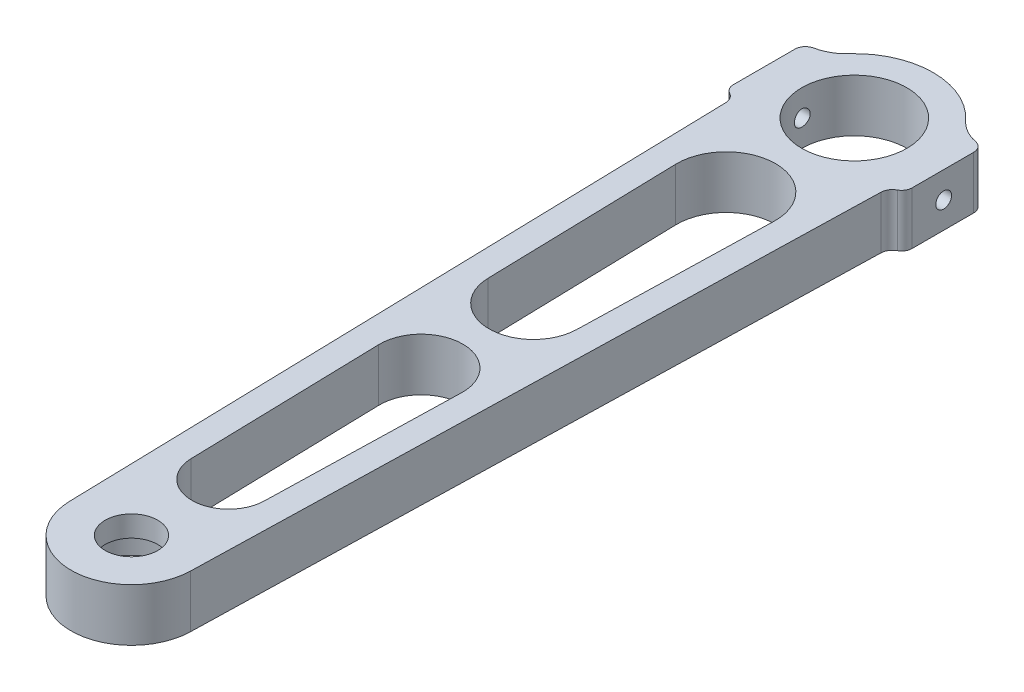
SolidWorks part; units mm, degrees
material "6061 Alloy"
ref_plane "Front Plane" through (0, 0, 0) normal (0, 0, 1) x (1, 0, 0)
ref_plane "Top Plane" through (0, 0, 0) normal (0, 1, 0) x (1, 0, 0)
ref_plane "Right Plane" through (0, 0, 0) normal (1, 0, 0) x (0, 0, -1)
sketch "Sketch1" plane through (0, 0, 0) normal (0, 1, 0) x (1, 0, 0)
  line L0 (-14.7582, -9.6854) -> (-11.4963, -137.7927)
  line L1 (14.7582, -9.6854) -> (11.4963, -137.7927)
  line L2 (-17, 7.5) -> (-17, -7.5)
  line L3 (17, 7.5) -> (17, -7.5)
  line L4 (-17, 0) -> (17, 0) construction
  circle A0 centre (0, 0) radius 10
  arc A1 (11.0789, 10.1122) -> (-11.0789, 10.1122) centre (0, 0) ccw
  arc A2 (-11.4963, -137.7927) -> (11.4963, -137.7927) centre (0, -137.5) ccw
  arc A3 (-17, 7.5) -> (-11.0789, 10.1122) centre (-17, 15.5167) ccw
  arc A4 (17, 7.5) -> (11.0789, 10.1122) centre (17, 15.5167) cw
  arc A5 (-17, -7.5) -> (-14.7582, -9.6854) centre (-17, -9.7425) cw
  arc A6 (17, -7.5) -> (14.7582, -9.6854) centre (17, -9.7425) ccw
  arc A7 (15, 0) -> (-15, 0) centre (0, 0) ccw construction
  point P10 (-17, 0)
  point P13 (17, 0)
  dimension "D1" = 20
  dimension "D2" = 30
  dimension "D3" = 23
  dimension "D5" = 15
  dimension "D4" = 137.5
  dimension "D6" = 2
  dimension "D7" = 2
extrude "Boss-Extrude1" add sketch "Sketch1" along normal blind 10
sketch "Sketch2" plane through (0, 0, 0) normal (0, 1, 0) x (1, 0, 0)
  circle A0 centre (0, -137.5) radius 9.5
  arc A1 (-11.4963, -137.7927) -> (11.4963, -137.7927) centre (0, -137.5) ccw construction
  dimension "D1" = 19
extrude "Cut-Extrude1" cut sketch "Sketch2" along normal blind 6
sketch "Sketch3" plane through (0, 0, 0) normal (0, -1, 0) x (-1, 0, 0)
  circle A0 centre (0, -137.5) radius 5
  arc A1 (-11.4963, -137.7927) -> (11.4963, -137.7927) centre (0, -137.5) ccw construction
  dimension "D1" = 10
extrude "Cut-Extrude2" cut sketch "Sketch3" against normal through all
sketch "Sketch4" plane through (0, 0, 0) normal (0, 1, 0) x (1, 0, 0)
  line L0 (-7.9005, -82.5806) -> (-6.9679, -119.2073)
  line L1 (7.9005, -82.5806) -> (6.9679, -119.2073)
  line L2 (0, -82.3794) -> (0, -119.0299) construction
  line L3 (-9.3764, -24.6182) -> (-8.4438, -61.2449)
  line L4 (9.3764, -24.6182) -> (8.4438, -61.2449)
  line L5 (11.4963, -137.7927) -> (14.7582, -9.6854) construction
  line L7 (0, -24.3794) -> (0, -61.0299) construction
  line L9 (11.4963, -137.7927) -> (14.7582, -9.6854) construction
  arc A0 (9.3764, -24.6182) -> (-9.3764, -24.6182) centre (0, -24.3794) ccw
  arc A1 (-8.4438, -61.2449) -> (8.4438, -61.2449) centre (0, -61.0299) ccw
  arc A2 (7.9005, -82.5806) -> (-7.9005, -82.5806) centre (0, -82.3794) ccw
  arc A3 (-6.9679, -119.2073) -> (6.9679, -119.2073) centre (0, -119.0299) ccw
  circle A4 centre (0, -137.5) radius 5 construction
  point P3 (0, -69.4764)
  point P18 (0, -74.4764)
  point P19 (0, -126)
  point P22 (0, -15)
  dimension "D1" = 15
  dimension "D2" = 5
  dimension "D3" = 11.5
  dimension "D4" = 5
extrude "Cut-Extrude4" cut sketch "Sketch4" along normal through all
fillet "Fillet1" radius 2 4 edges at (-17, 5, -7.5) (-17, 5, 7.5) (17, 5, 7.5) (17, 5, -7.5)
hole_wizard "M4 Tapped Hole1" positions "Sketch5" profile "Sketch6" tap size "M4" standard "ISO" end condition through all
sketch "Sketch5" plane through (-17, 0, 0) normal (-1, 0, 0) x (0, 0, 1)
  point P0 (0, 5)
  dimension "D1" = 5
sketch "Sketch6" plane through (-17, 5, 0) normal (0, 1, 0) x (0, 0, 1)
  line L0 (0, 0) -> (0, 34)
  line L1 (0, 34) -> (1.5, 34)
  line L2 (1.5, 34) -> (1.5, 0)
  line L5 (1.5, 0) -> (0, 0)
  line L11 (0, -6.35) -> (0, 107.95) construction
  dimension "Thru Tap Drill Dia." = 3
  dimension "Thru Tap Drill Depth" = 34
cosmetic thread "Hole Thread1" parameters "D2"=4
